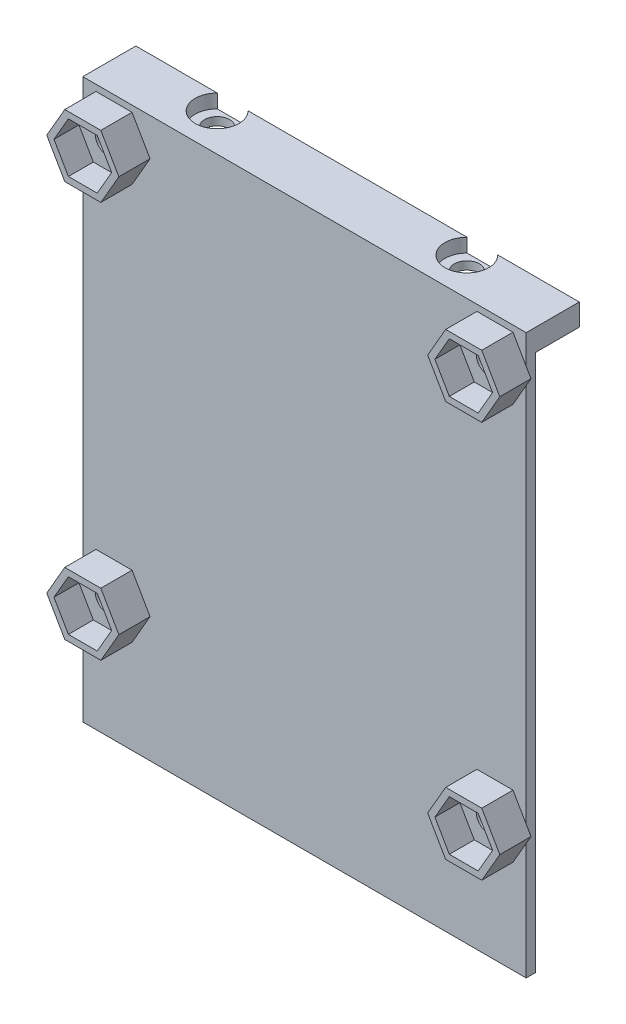
SolidWorks part; units mm, degrees
material "PLA_printed_black"
ref_plane "Front Plane" through (0, 0, 0) normal (0, 0, 1) x (1, 0, 0)
ref_plane "Top Plane" through (0, 0, 0) normal (0, 1, 0) x (1, 0, 0)
ref_plane "Right Plane" through (0, 0, 0) normal (1, 0, 0) x (0, 0, -1)
sketch "Sketch2" plane through (0, 0, 0) normal (0, 0, 1) x (1, 0, 0)
  line L1 (0, 0) -> (71, 0)
  line L2 (0, 0) -> (0, 73.5)
  line L3 (0, 73.5) -> (71, 73.5)
  line L4 (71, 0) -> (71, 73.5)
  dimension "D1" = 71
  dimension "D2" = 73.5
extrude "Boss-Extrude1" add sketch "Sketch2" along normal blind 1.5
sketch "Sketch3" plane through (0, 0, 1.5) normal (0, 0, 1) x (1, 0, 0)
  line L4 (0, 73.5) -> (0, 0) construction
  line L5 (10.7735, 68.5) -> (7.8868, 73.5)
  line L6 (7.8868, 73.5) -> (2.1132, 73.5)
  line L7 (2.1132, 73.5) -> (-0.7735, 68.5)
  line L8 (-0.7735, 68.5) -> (2.1132, 63.5)
  line L9 (2.1132, 63.5) -> (7.8868, 63.5)
  line L10 (7.8868, 63.5) -> (10.7735, 68.5)
  line L11 (71, 73.5) -> (0, 73.5) construction
  line L12 (35.5, 73.5) -> (35.5, 0) construction
  line L13 (0, 0) -> (71, 0) construction
  line L14 (0, 36.75) -> (71, 36.75) construction
  line L15 (71, 0) -> (71, 73.5) construction
  line L16 (63.1132, 63.5) -> (60.2265, 68.5)
  line L17 (68.8868, 63.5) -> (63.1132, 63.5)
  line L18 (71.7735, 68.5) -> (68.8868, 63.5)
  line L19 (68.8868, 73.5) -> (71.7735, 68.5)
  line L20 (63.1132, 73.5) -> (68.8868, 73.5)
  line L21 (60.2265, 68.5) -> (63.1132, 73.5)
  line L22 (60.2265, 5) -> (63.1132, 0)
  line L23 (63.1132, 0) -> (68.8868, 0)
  line L24 (68.8868, 0) -> (71.7735, 5)
  line L25 (71.7735, 5) -> (68.8868, 10)
  line L26 (68.8868, 10) -> (63.1132, 10)
  line L27 (63.1132, 10) -> (60.2265, 5)
  line L28 (7.8868, 10) -> (10.7735, 5)
  line L29 (2.1132, 10) -> (7.8868, 10)
  line L30 (-0.7735, 5) -> (2.1132, 10)
  line L31 (2.1132, 0) -> (-0.7735, 5)
  line L32 (7.8868, 0) -> (2.1132, 0)
  line L33 (10.7735, 5) -> (7.8868, 0)
  circle A4 centre (5, 68.5) radius 5 construction
  circle A5 centre (66, 68.5) radius 5 construction
  circle A6 centre (66, 5) radius 5 construction
  circle A7 centre (5, 5) radius 5 construction
  point P17 (5, 68.5)
  dimension "D1" = 10
  dimension "D2" = 5
  dimension "D3" = 5
extrude "Boss-Extrude2" add sketch "Sketch3" along normal blind 5
sketch "Sketch20" plane through (0, 0, 1.5) normal (0, 0, 1) x (1, 0, 0)
  line L0 (0, 73.5) -> (0, 69.8397) construction
  line L1 (71, 73.5) -> (0, 73.5)
  line L2 (71, 73.5) -> (71, 74.5)
  line L3 (71, 74.5) -> (0, 74.5)
  line L4 (0, 73.5) -> (0, 74.5)
  dimension "D1" = 1
extrude "Boss-Extrude6" add sketch "Sketch20" against normal up to surface (1.5 mm away)
sketch "Sketch12" plane through (0, 74.5, 0) normal (0, -1, 0) x (1, 0, 0)
  line L0 (0, 0) -> (71, 0) construction
  line L1 (71, 0) -> (0, 0)
  line L2 (71, 0) -> (71, -7)
  line L3 (71, -7) -> (0, -7)
  line L4 (0, 0) -> (0, -7)
  line L5 (71, 1.5) -> (71, 0) construction
  dimension "D1" = 7
extrude "Boss-Extrude3" add sketch "Sketch12" along normal blind 3.5
sketch "Sketch13" plane through (0, 0, 0) normal (0, -1, 0) x (1, 0, 0)
  line L0 (0, -7) -> (71, -7) construction
  line L2 (55.5, -4.5) -> (15.5, -4.5) construction
  circle A0 centre (55.5, -4.5) radius 2
  circle A1 centre (15.5, -4.5) radius 2
  point P6 (35.5, -4.5)
  point P7 (35.5, -7)
  dimension "D1" = 40
  dimension "D2" = 2.5
  dimension "D3" = 4
extrude "Cut-Extrude3" cut sketch "Sketch13" against normal through all
sketch "Sketch14" plane through (0, 74.5, 0) normal (0, -1, 0) x (-1, 0, 0)
  circle A0 centre (-55.5, 4.5) radius 3.5
  circle A1 centre (-15.5, 4.5) radius 3.5
  dimension "D1" = 7
extrude "Cut-Extrude4" cut sketch "Sketch14" along normal blind 2.2
sketch "Sketch15" plane through (0, 0, 0) normal (0, -1, 0) x (1, 0, 0)
  line L1 (0, 0) -> (71, 0)
  line L2 (0, 0) -> (0, 1.5)
  line L3 (0, 1.5) -> (71, 1.5)
  line L4 (71, 0) -> (71, 1.5)
extrude "Boss-Extrude4" add sketch "Sketch15" along normal blind 15
sketch "Sketch16" plane through (0, 0, 1.5) normal (0, 0, 1) x (1, 0, 0)
  line L0 (0, 67.1603) -> (0, 6.3397) construction
  line L1 (71, 73.5) -> (0, 73.5) construction
  circle A0 centre (35.5, -10.5) radius 4
  circle A1 centre (35.5, -10.5) radius 2.75
  dimension "D1" = 84
  dimension "D2" = 5.5
  dimension "D3" = 8
  dimension "D4" = 35.5
extrude "Boss-Extrude5" add sketch "Sketch16" against normal offset from surface (4.5 mm away) 3
sketch "Sketch17" plane through (0, 0, 6.5) normal (0, 0, 1) x (1, 0, 0)
  line L0 (7.8868, 73.5) -> (2.1132, 73.5) construction
  line L1 (7.3094, 72.5) -> (2.6906, 72.5)
  line L2 (2.6906, 72.5) -> (0.3812, 68.5)
  line L3 (0.3812, 68.5) -> (2.6906, 64.5)
  line L4 (2.6906, 64.5) -> (7.3094, 64.5)
  line L5 (7.3094, 64.5) -> (9.6188, 68.5)
  line L6 (9.6188, 68.5) -> (7.3094, 72.5)
  line L7 (0.3812, 68.5) -> (9.6188, 68.5) construction
  line L8 (-0.7735, 68.5) -> (10.7735, 68.5) construction
  line L10 (68.3094, 72.5) -> (63.6906, 72.5)
  line L11 (63.6906, 72.5) -> (61.3812, 68.5)
  line L12 (61.3812, 68.5) -> (63.6906, 64.5)
  line L13 (63.6906, 64.5) -> (68.3094, 64.5)
  line L14 (68.3094, 64.5) -> (70.6188, 68.5)
  line L15 (70.6188, 68.5) -> (68.3094, 72.5)
  line L16 (68.3094, 9) -> (63.6906, 9)
  line L17 (63.6906, 9) -> (61.3812, 5)
  line L18 (61.3812, 5) -> (63.6906, 1)
  line L19 (63.6906, 1) -> (68.3094, 1)
  line L20 (68.3094, 1) -> (70.6188, 5)
  line L21 (70.6188, 5) -> (68.3094, 9)
  line L22 (7.3094, 9) -> (2.6906, 9)
  line L23 (2.6906, 9) -> (0.3812, 5)
  line L24 (0.3812, 5) -> (2.6906, 1)
  line L25 (2.6906, 1) -> (7.3094, 1)
  line L26 (7.3094, 1) -> (9.6188, 5)
  line L27 (9.6188, 5) -> (7.3094, 9)
  circle A0 centre (5, 68.5) radius 4 construction
  point P10 (5, 73.5)
  point P11 (66, 68.5)
  dimension "D1" = 8
  dimension "D2" = 2
  dimension "D3" = 2
extrude "Cut-Extrude5" cut sketch "Sketch17" against normal blind 4
sketch "Sketch19" plane through (0, 0, 6.5) normal (0, 0, 1) x (1, 0, 0)
  circle A0 centre (5, 68.5) radius 2
  circle A1 centre (66, 68.5) radius 2
  circle A2 centre (5, 5) radius 2
  circle A3 centre (66, 5) radius 2
  dimension "D1" = 4
extrude "Cut-Extrude6" cut sketch "Sketch19" against normal through all
